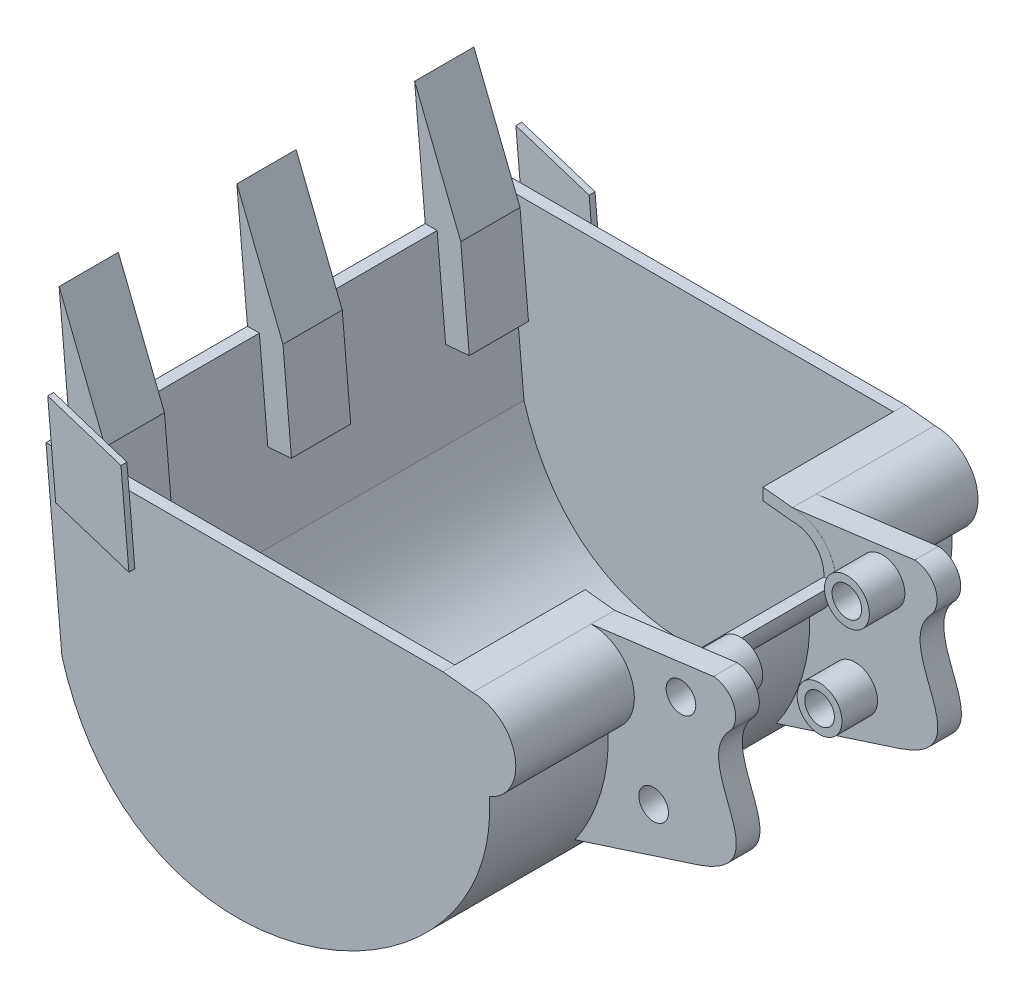
SolidWorks part; units mm, degrees
ref_plane "Front Plane" through (0, 0, 0) normal (0, 0, 1) x (1, 0, 0)
ref_plane "Top Plane" through (0, 0, 0) normal (0, 1, 0) x (1, 0, 0)
ref_plane "Right Plane" through (0, 0, 0) normal (1, 0, 0) x (0, 0, -1)
sketch "Sketch1" plane through (0, 0, 0) normal (0, 0, 1) x (1, 0, 0)
  line L0 (130, 0) -> (-130, 0)
  line L9 (130, 0) -> (130, -80) construction
  line L12 (130, 0) -> (154.8586, -2.6547)
  line L14 (-191.5919, -149.3995) -> (130, -80) construction
  line L17 (-130, 0) -> (-205, 0)
  line L18 (-205, 0) -> (-191.5919, -149.3995)
  line L19 (130, -80) -> (169.0999, -71.5622) construction
  line L20 (-30.7959, -114.6998) -> (0.8457, -261.3245) construction
  arc A3 (154.8586, -2.6547) -> (169.0999, -71.5622) centre (155.6323, -38.4202) cw
  spline S0 degree 3 poles (-191.5919, -149.3995) (-126.4253, -370.0907) (179.8541, -241.3594) (169.0999, -71.5622) knots 0 0 0 0 1 1 1 1
  point P4 (0, 0)
  dimension "D6" = 260
  dimension "D7" = 25
extrude "Basic_geometry" add sketch "Sketch1" along normal mid plane 390
shell "Remove_material" thickness 10
sketch "Sketch2" plane through (0, 0, 0) normal (0, 1, 0) x (1, 0, 0)
  line L0 (35.8281, -185) -> (130, -185)
  line L3 (130, -195) -> (130, 195) construction
  line L5 (159.3763, -185) -> (-181.7215, -185) construction
  line L6 (130, -185) -> (130, 185)
  line L8 (-181.7215, 185) -> (159.3763, 185) construction
  line L9 (130, 185) -> (35.8281, 185)
  line L10 (35.8281, 185) -> (35.8281, -185)
sketch "Sketch7" plane through (0, 0, -185) normal (0, 0, 1) x (1, 0, 0)
  line L9 (-205, 0) -> (-213.9387, 99.5997)
  line L10 (-205, 0) -> (-194.9598, 0)
  line L11 (-194.9598, 0) -> (-187.8088, -79.6798)
  line L12 (-194.9598, 0) -> (-181.7215, -147.5077) construction
  line L13 (-187.8088, -79.6798) -> (-167.8889, -77.892)
  line L14 (-167.8889, -77.892) -> (-175.0399, 1.7877)
  line L15 (-213.9387, 99.5997) -> (-175.0399, 1.7877)
extrude "Teeth" add sketch "Sketch7" along normal blind 50 from offset 10
extrude "Remove_material2" cut sketch "Sketch2" against normal blind 50
pattern_linear "Teeth_pattern" count 3 spacing 150 along (0, 0, 1) of "Teeth"
sketch "Sketch8" plane through (0, 0, 195) normal (0, 0, 1) x (1, 0, 0)
  line L0 (-194.9598, 0) -> (-198.5353, 39.8399)
  line L1 (-194.9598, 0) -> (-134.9598, 0) construction
  line L2 (130, 0) -> (-205, 0) construction
  line L5 (-194.9598, 0) -> (-191.8312, -34.8599)
  line L6 (-134.9598, 0) -> (-136.7476, 19.9199)
  line L7 (-198.5353, 39.8399) -> (-136.7476, 19.9199)
  line L8 (-134.9598, 0) -> (-130.0435, -54.7798)
  line L9 (-191.8312, -34.8599) -> (-130.0435, -54.7798)
extrude "Side_plate" add sketch "Sketch8" along normal blind 5
mirror "Side_plate_mirror" about plane through (0, 0, 0) normal (0, 0, 1) of "Side_plate"
sketch "Sketch9" plane through (0, 0, 0) normal (0, 0, 1) x (1, 0, 0)
  line L0 (141.2967, -167.0571) -> (245.9674, -133.2334)
  line L1 (154.8586, -2.6547) -> (258.0999, 10.6957)
  arc A2 (154.8586, -2.6547) -> (169.0999, -71.5622) centre (155.6323, -38.4202) cw
  arc A3 (169.0999, -71.5622) -> (141.2967, -167.0571) centre (14.1795, -78.2523) cw
  arc A4 (258.0999, 10.6957) -> (272.5947, -21.4623) centre (256.9746, -9.1572) cw
  spline S0 degree 3 poles (-191.5919, -149.3995) (-126.4253, -370.0907) (179.8541, -241.3594) (169.0999, -71.5622) knots 0 0 0 0 1 1 1 1 construction
  spline S1 degree 3 poles (272.5947, -21.4623) (235.1132, -59.3334) (319.8726, -107.999) (245.9674, -133.2334) knots 0 0 0 0 1 1 1 1
extrude "Boss-Extrude6" add sketch "Sketch9" along direction (0, 0, 1) on the side of the normal blind 20 from offset 75 separate body
pattern_linear "LPattern4" count 2 spacing 170 along (0, 0, 1) of "Boss-Extrude6"
sketch "Sketch10" plane through (0, 0, 95) normal (0, 0, 1) x (1, 0, 0)
  line L0 (207.704, -108.0476) -> (230.3763, -108.0476) construction
  line L1 (258.0999, 10.6957) -> (154.8586, -2.6547) construction
  line L2 (-213.9387, 99.5997) -> (230.7624, -18.0476) construction
  line L3 (-213.9387, 99.5997) -> (207.704, -108.0476) construction
  circle A1 centre (230.7624, -18.0476) radius 12.5
  circle A2 centre (207.704, -108.0476) radius 12.5
  point P8 (0, 0)
  point P10 (0, 0)
  dimension "D1" = 25
  dimension "D2" = 25
  dimension "D3" = 90
  dimension "D4" = 25
  dimension "D5" = 460
  dimension "D6" = 470
extrude "Cut-Extrude4" cut sketch "Sketch10" against normal through all
sketch "Sketch11" plane through (0, 0, 75) normal (0, 0, -1) x (-1, 0, 0)
  circle A1 centre (-230.7624, -18.0476) radius 18.9115
  circle A2 centre (-230.7624, -18.0476) radius 12.5
  circle A3 centre (-207.704, -108.0476) radius 18.9115
  circle A4 centre (-207.704, -108.0476) radius 12.5
extrude "Boss-Extrude7" add sketch "Sketch11" along normal blind 30
pattern_linear "LPattern7" count 2 spacing 120 along (0, 0, -1) of "Boss-Extrude7"
sketch "Sketch13" plane through (130, 0, 0) normal (-1, 0, 0) x (0, 0, 1)
  line L0 (-25, 0) -> (-125, 0) construction
  line L1 (-75, 0) -> (75, 0)
  line L2 (-75, 0) -> (-75, -40)
  line L3 (-75, -40) -> (75, -40)
  line L4 (75, 0) -> (75, -40)
extrude "Cut-Extrude5" cut sketch "Sketch13" against normal blind 70
